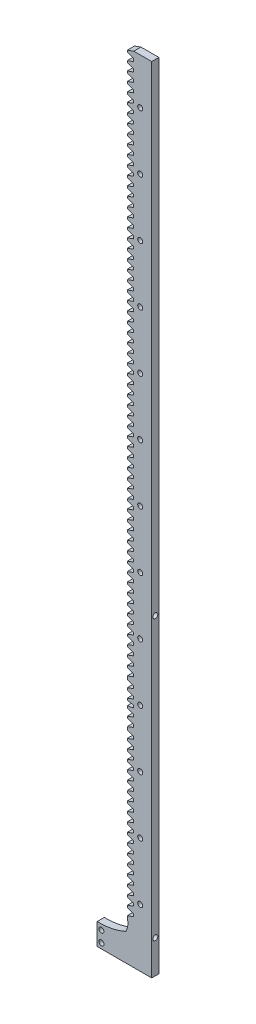
SolidWorks part; units mm, degrees
ref_plane "前视基准面" through (0, 0, 0) normal (0, 0, 1) x (1, 0, 0)
ref_plane "上视基准面" through (0, 0, 0) normal (0, 1, 0) x (1, 0, 0)
ref_plane "右视基准面" through (0, 0, 0) normal (1, 0, 0) x (0, 0, -1)
sketch "草图1" plane through (0, 0, 0) normal (0, 0, 1) x (1, 0, 0)
  line L0 (0, 0) -> (-38, 0)
  line L1 (-38, 0) -> (-38, 15)
  line L2 (-38, 15) -> (-10, 15) construction
  line L3 (-10, 95) -> (-10, 300) construction
  line L4 (-10, 300) -> (0, 300) construction
  line L5 (0, 300) -> (0, 0)
  line L6 (-12.5, 158.072) -> (-12.5, 156.352)
  line L7 (-12.5, 157.212) -> (-8.1615, 157.212) construction
  line L8 (-17, 143.0077) -> (-12.5, 144.6456)
  line L9 (-12.5, 139.2262) -> (-17, 140.864)
  line L10 (-12.5, 137.5024) -> (-12.5, 139.2262)
  line L11 (-17, 135.8646) -> (-12.5, 137.5024)
  line L12 (-17, 134.5808) -> (-17, 135.8646)
  line L13 (-12.5, 132.943) -> (-17, 134.5808)
  line L14 (-12.5, 131.2192) -> (-12.5, 132.943)
  line L15 (-17, 129.5814) -> (-12.5, 131.2192)
  line L16 (-17, 128.2977) -> (-17, 129.5814)
  line L17 (-12.5, 126.6598) -> (-17, 128.2977)
  line L18 (-12.5, 124.9361) -> (-12.5, 126.6598)
  line L19 (-17, 123.2982) -> (-12.5, 124.9361)
  line L20 (-17, 122.0145) -> (-17, 123.2982)
  line L21 (-12.5, 120.3766) -> (-17, 122.0145)
  line L22 (-12.5, 118.6529) -> (-12.5, 120.3766)
  line L23 (-17, 117.015) -> (-12.5, 118.6529)
  line L24 (-17, 115.7313) -> (-17, 117.015)
  line L25 (-12.5, 114.0934) -> (-17, 115.7313)
  line L26 (-12.5, 112.3697) -> (-12.5, 114.0934)
  line L27 (-17, 110.7318) -> (-12.5, 112.3697)
  line L28 (-17, 109.4481) -> (-17, 110.7318)
  line L29 (-12.5, 107.8102) -> (-17, 109.4481)
  line L30 (-12.5, 106.0865) -> (-12.5, 107.8102)
  line L31 (-17, 104.4486) -> (-12.5, 106.0865)
  line L32 (-17, 103.1649) -> (-17, 104.4486)
  line L33 (-12.5, 101.5271) -> (-17, 103.1649)
  line L34 (-12.5, 99.8033) -> (-12.5, 101.5271)
  line L35 (-17, 98.1654) -> (-12.5, 99.8033)
  line L36 (-17, 96.8817) -> (-17, 98.1654)
  line L37 (-12.5, 95.2439) -> (-17, 96.8817)
  line L38 (-12.5, 93.5201) -> (-12.5, 95.2439)
  line L39 (-17, 91.8823) -> (-12.5, 93.5201)
  line L40 (-17, 90.5985) -> (-17, 91.8823)
  line L41 (-12.5, 88.9607) -> (-17, 90.5985)
  line L42 (-12.5, 87.2369) -> (-12.5, 88.9607)
  line L43 (-17, 85.5991) -> (-12.5, 87.2369)
  line L44 (-17, 84.3154) -> (-17, 85.5991)
  line L45 (-12.5, 82.6775) -> (-17, 84.3154)
  line L46 (-12.5, 80.9538) -> (-12.5, 82.6775)
  line L47 (-17, 79.3159) -> (-12.5, 80.9538)
  line L48 (-17, 78.0322) -> (-17, 79.3159)
  line L49 (-12.5, 76.3943) -> (-17, 78.0322)
  line L50 (-12.5, 74.6706) -> (-12.5, 76.3943)
  line L51 (-17, 73.0327) -> (-12.5, 74.6706)
  line L52 (-17, 71.749) -> (-17, 73.0327)
  line L53 (-12.5, 70.1111) -> (-17, 71.749)
  line L54 (-12.5, 68.3874) -> (-12.5, 70.1111)
  line L55 (-17, 66.7495) -> (-12.5, 68.3874)
  line L56 (-17, 65.4658) -> (-17, 66.7495)
  line L57 (-12.5, 63.8279) -> (-17, 65.4658)
  line L58 (-12.5, 62.1042) -> (-12.5, 63.8279)
  line L59 (-17, 60.4663) -> (-12.5, 62.1042)
  line L60 (-17, 59.1826) -> (-17, 60.4663)
  line L61 (-12.5, 57.5448) -> (-17, 59.1826)
  line L62 (-12.5, 55.821) -> (-12.5, 57.5448)
  line L63 (-17, 54.1831) -> (-12.5, 55.821)
  line L64 (-17, 52.8994) -> (-17, 54.1831)
  line L65 (-12.5, 51.2616) -> (-17, 52.8994)
  line L66 (-12.5, 49.5378) -> (-12.5, 51.2616)
  line L67 (-17, 47.9) -> (-12.5, 49.5378)
  line L68 (-17, 46.6163) -> (-17, 47.9)
  line L69 (-12.5, 44.9784) -> (-17, 46.6163)
  line L70 (-12.5, 43.2546) -> (-12.5, 44.9784)
  line L71 (-17, 41.6168) -> (-12.5, 43.2546)
  line L72 (-17, 40.3331) -> (-17, 41.6168)
  line L73 (-12.5, 38.6952) -> (-17, 40.3331)
  line L74 (-12.5, 36.9715) -> (-12.5, 38.6952)
  line L75 (-17, 35.3336) -> (-12.5, 36.9715)
  line L76 (-17, 34.0499) -> (-17, 35.3336)
  line L77 (-12.5, 32.412) -> (-17, 34.0499)
  line L78 (-12.5, 30.6883) -> (-12.5, 32.412)
  line L79 (-17, 29.0504) -> (-12.5, 30.6883)
  line L80 (-17, 27.7667) -> (-17, 29.0504)
  line L81 (-12.5, 300.8615) -> (-12.5, 301.7215)
  line L82 (-12.5, 301.7215) -> (-10, 301.7215) construction
  line L83 (-12.5, 332.2737) -> (-12.5, 333.9937)
  line L84 (-17, 143.0077) -> (-17, 140.864)
  line L85 (-12.5, 300.8615) -> (-10, 300) construction
  line L86 (0, 332.2737) -> (0, 300)
  line L87 (-12.5, 333.1337) -> (-6.574, 333.1337) construction
  line L88 (-12.5, 338.5531) -> (-12.5, 340.2731)
  line L89 (-12.5, 339.4131) -> (-30.4802, 339.4131) construction
  line L90 (-12.5, 144.6456) -> (-12.5, 146.3694)
  line L91 (-12.5, 146.3694) -> (-17, 148.0072)
  line L92 (-17, 148.0072) -> (-17, 149.2909)
  line L93 (-17, 149.2909) -> (-12.5, 150.9288)
  line L94 (-12.5, 150.9288) -> (-12.5, 152.6525)
  line L95 (-12.5, 152.6525) -> (-17, 154.2904)
  line L96 (-17, 154.2904) -> (-17, 155.5741)
  line L97 (-17, 155.5741) -> (-12.5, 156.352)
  line L98 (-12.5, 338.5531) -> (-17, 336.9153)
  line L99 (-17, 336.9153) -> (-17, 335.6316)
  line L100 (-17, 335.6316) -> (-12.5, 333.9937)
  line L101 (-17, 406.0191) -> (-12.5, 407.6569)
  line L102 (-17, 404.7354) -> (-17, 406.0191)
  line L103 (0, 345.3332) -> (0, 332.2737)
  line L104 (-17, 330.6358) -> (-12.5, 332.2737)
  line L105 (-17, 329.3521) -> (-17, 330.6358)
  line L106 (-12.5, 327.7142) -> (-17, 329.3521)
  line L107 (-12.5, 325.9905) -> (-12.5, 327.7142)
  line L108 (-17, 324.3526) -> (-12.5, 325.9905)
  line L109 (-17, 323.0689) -> (-17, 324.3526)
  line L110 (-12.5, 321.4311) -> (-17, 323.0689)
  line L111 (-12.5, 319.7073) -> (-12.5, 321.4311)
  line L112 (-17, 318.0694) -> (-12.5, 319.7073)
  line L113 (-17, 316.7857) -> (-17, 318.0694)
  line L114 (-12.5, 315.1479) -> (-17, 316.7857)
  line L115 (-12.5, 313.4241) -> (-12.5, 315.1479)
  line L116 (-17, 311.7863) -> (-12.5, 313.4241)
  line L117 (-17, 310.5026) -> (-17, 311.7863)
  line L118 (-12.5, 308.8647) -> (-17, 310.5026)
  line L119 (-12.5, 307.1409) -> (-12.5, 308.8647)
  line L120 (-17, 305.5031) -> (-12.5, 307.1409)
  line L121 (-17, 304.2194) -> (-17, 305.5031)
  line L122 (-12.5, 302.5815) -> (-17, 304.2194)
  line L123 (-12.5, 302.5815) -> (-12.5, 301.7215)
  line L124 (-12.5, 403.0975) -> (-17, 404.7354)
  line L125 (-12.5, 401.3738) -> (-12.5, 403.0975)
  line L126 (-17, 399.7359) -> (-12.5, 401.3738)
  line L127 (-17, 398.4522) -> (-17, 399.7359)
  line L128 (-12.5, 396.8143) -> (-17, 398.4522)
  line L129 (-12.5, 395.0906) -> (-12.5, 396.8143)
  line L130 (-17, 393.4527) -> (-12.5, 395.0906)
  line L131 (-17, 392.169) -> (-17, 393.4527)
  line L132 (-12.5, 390.5311) -> (-17, 392.169)
  line L133 (-12.5, 388.8074) -> (-12.5, 390.5311)
  line L134 (-17, 387.1695) -> (-12.5, 388.8074)
  line L135 (-17, 385.8858) -> (-17, 387.1695)
  line L136 (-12.5, 384.2479) -> (-17, 385.8858)
  line L137 (-12.5, 382.5242) -> (-12.5, 384.2479)
  line L138 (-17, 380.8863) -> (-12.5, 382.5242)
  line L139 (-17, 379.6026) -> (-17, 380.8863)
  line L140 (-12.5, 377.9648) -> (-17, 379.6026)
  line L141 (-12.5, 376.2448) -> (-12.5, 377.1048)
  line L142 (-12.5, 376.2448) -> (-17, 374.6069)
  line L143 (-17, 374.6069) -> (-17, 373.3232)
  line L144 (-17, 373.3232) -> (-12.5, 371.6853)
  line L145 (-12.5, 371.6853) -> (-12.5, 369.9616)
  line L146 (-12.5, 369.9616) -> (-17, 368.3237)
  line L147 (-17, 368.3237) -> (-17, 367.04)
  line L148 (-17, 367.04) -> (-12.5, 365.4021)
  line L149 (-12.5, 365.4021) -> (-12.5, 363.6784)
  line L150 (-12.5, 363.6784) -> (-17, 362.0405)
  line L151 (-17, 362.0405) -> (-17, 360.7568)
  line L152 (-17, 360.7568) -> (-12.5, 359.1189)
  line L153 (-12.5, 359.1189) -> (-12.5, 357.3952)
  line L154 (-12.5, 357.3952) -> (-17, 355.7573)
  line L155 (-17, 355.7573) -> (-17, 354.4736)
  line L156 (-17, 354.4736) -> (-12.5, 352.8358)
  line L157 (-12.5, 352.8358) -> (-12.5, 351.112)
  line L158 (-12.5, 351.112) -> (-17, 349.4742)
  line L159 (-17, 349.4742) -> (-17, 348.1904)
  line L160 (-17, 348.1904) -> (-12.5, 346.5526)
  line L161 (-12.5, 346.5526) -> (-12.5, 344.8326)
  line L162 (-17, 343.1947) -> (-12.5, 344.8326)
  line L163 (-17, 341.911) -> (-17, 343.1947)
  line L164 (-12.5, 340.2731) -> (-17, 341.911)
  line L165 (-12.5, 407.6569) -> (-12.5, 409.3769)
  line L166 (-12.5, 408.5169) -> (-23.385, 408.5169) construction
  line L167 (-12.5, 377.9648) -> (-12.5, 377.1048)
  line L168 (-12.5, 439.0691) -> (-12.5, 439.9291)
  line L169 (-12.5, 452.4936) -> (-35.8093, 452.4936) construction
  line L170 (-12.5, 483.9058) -> (-28.5245, 483.9058) construction
  line L171 (-12.5, 451.6318) -> (-12.5, 453.3555)
  line L172 (-17, 449.9939) -> (-12.5, 451.6318)
  line L173 (-17, 448.7102) -> (-17, 449.9939)
  line L174 (-12.5, 447.0723) -> (-17, 448.7102)
  line L175 (-12.5, 445.3486) -> (-12.5, 447.0723)
  line L176 (-17, 443.7107) -> (-12.5, 445.3486)
  line L177 (-17, 442.427) -> (-17, 443.7107)
  line L178 (-12.5, 440.7891) -> (-17, 442.427)
  line L179 (-12.5, 440.7891) -> (-12.5, 439.9291)
  line L180 (-12.5, 439.0691) -> (-17, 437.4313)
  line L181 (-17, 437.4313) -> (-17, 436.1476)
  line L182 (-17, 436.1476) -> (-12.5, 434.5097)
  line L183 (-12.5, 434.5097) -> (-12.5, 432.7859)
  line L184 (-12.5, 432.7859) -> (-17, 431.1481)
  line L185 (-17, 431.1481) -> (-17, 429.8644)
  line L186 (-17, 429.8644) -> (-12.5, 428.2265)
  line L187 (-12.5, 428.2265) -> (-12.5, 426.5028)
  line L188 (-12.5, 426.5028) -> (-17, 424.8649)
  line L189 (-17, 424.8649) -> (-17, 423.5812)
  line L190 (-17, 423.5812) -> (-12.5, 421.9433)
  line L191 (-12.5, 421.9433) -> (-12.5, 420.2196)
  line L192 (-12.5, 420.2196) -> (-17, 418.5817)
  line L193 (-17, 418.5817) -> (-17, 417.298)
  line L194 (-17, 417.298) -> (-12.5, 415.6601)
  line L195 (-12.5, 415.6601) -> (-12.5, 413.9364)
  line L196 (-12.5, 413.9364) -> (-17, 412.2985)
  line L197 (-17, 412.2985) -> (-17, 411.0148)
  line L198 (-17, 411.0148) -> (-12.5, 409.3769)
  line L199 (-12.5, 515.318) -> (-35.8093, 515.318) construction
  line L200 (-12.5, 483.0439) -> (-12.5, 484.7677)
  line L201 (-17, 481.4061) -> (-12.5, 483.0439)
  line L202 (-17, 480.1224) -> (-17, 481.4061)
  line L203 (-12.5, 478.4845) -> (-17, 480.1224)
  line L204 (-12.5, 476.7608) -> (-12.5, 478.4845)
  line L205 (-17, 475.1229) -> (-12.5, 476.7608)
  line L206 (-17, 473.8392) -> (-17, 475.1229)
  line L207 (-12.5, 472.2013) -> (-17, 473.8392)
  line L208 (-12.5, 470.4776) -> (-12.5, 472.2013)
  line L209 (-17, 468.8397) -> (-12.5, 470.4776)
  line L210 (-17, 467.556) -> (-17, 468.8397)
  line L211 (-12.5, 465.9181) -> (-17, 467.556)
  line L212 (-12.5, 464.1981) -> (-12.5, 465.0581)
  line L213 (-12.5, 464.1981) -> (-17, 462.5603)
  line L214 (-17, 462.5603) -> (-17, 461.2766)
  line L215 (-17, 461.2766) -> (-12.5, 459.6387)
  line L216 (-12.5, 459.6387) -> (-12.5, 457.9149)
  line L217 (-12.5, 457.9149) -> (-17, 456.2771)
  line L218 (-17, 456.2771) -> (-17, 454.9934)
  line L219 (-17, 454.9934) -> (-12.5, 453.3555)
  line L220 (-12.5, 465.9181) -> (-12.5, 465.0581)
  line L221 (-12.5, 501.8935) -> (-12.5, 502.7535)
  line L222 (-17, 512.8183) -> (-12.5, 514.4561)
  line L223 (-17, 511.5346) -> (-17, 512.8183)
  line L224 (-12.5, 509.8967) -> (-17, 511.5346)
  line L225 (-12.5, 508.1729) -> (-12.5, 509.8967)
  line L226 (-17, 506.5351) -> (-12.5, 508.1729)
  line L227 (-17, 505.2514) -> (-17, 506.5351)
  line L228 (-12.5, 503.6135) -> (-17, 505.2514)
  line L229 (-12.5, 503.6135) -> (-12.5, 502.7535)
  line L230 (-12.5, 501.8935) -> (-17, 500.2556)
  line L231 (-17, 500.2556) -> (-17, 498.9719)
  line L232 (-17, 498.9719) -> (-12.5, 497.3341)
  line L233 (-12.5, 497.3341) -> (-12.5, 495.6103)
  line L234 (-12.5, 495.6103) -> (-17, 493.9724)
  line L235 (-17, 493.9724) -> (-17, 492.6887)
  line L236 (-17, 492.6887) -> (-12.5, 491.0509)
  line L237 (-12.5, 491.0509) -> (-12.5, 489.3271)
  line L238 (-12.5, 489.3271) -> (-17, 487.6893)
  line L239 (-17, 487.6893) -> (-17, 486.4056)
  line L240 (-17, 486.4056) -> (-12.5, 484.7677)
  line L241 (0, 345.3332) -> (0, 552.1515)
  line L242 (0, 552.1515) -> (-12.5, 552.1515)
  line L243 (-17, 550.5136) -> (-12.5, 552.1515)
  line L244 (-17, 549.2299) -> (-17, 550.5136)
  line L245 (-12.5, 547.5921) -> (-17, 549.2299)
  line L246 (-12.5, 545.8683) -> (-12.5, 547.5921)
  line L247 (-17, 544.2304) -> (-12.5, 545.8683)
  line L248 (-17, 542.9467) -> (-17, 544.2304)
  line L249 (-12.5, 541.3089) -> (-17, 542.9467)
  line L250 (-12.5, 539.5851) -> (-12.5, 541.3089)
  line L251 (-17, 537.9473) -> (-12.5, 539.5851)
  line L252 (-17, 536.6635) -> (-17, 537.9473)
  line L253 (-12.5, 535.0257) -> (-17, 536.6635)
  line L254 (-10.0528, 23.9832) -> (-10.0528, 22.8309) construction
  line L255 (-12.5, 533.3019) -> (-12.5, 535.0257)
  line L256 (-17, 531.6641) -> (-12.5, 533.3019)
  line L257 (-17, 530.3804) -> (-17, 531.6641)
  line L258 (-12.5, 528.7425) -> (-17, 530.3804)
  line L259 (-12.5, 527.0225) -> (-12.5, 527.8825)
  line L260 (-12.5, 527.0225) -> (-17, 525.3846)
  line L261 (-17, 525.3846) -> (-17, 524.1009)
  line L262 (-17, 524.1009) -> (-12.5, 522.4631)
  line L263 (-12.5, 522.4631) -> (-12.5, 520.7393)
  line L264 (-18.0028, 31.7521) -> (-18.0028, -9.9201) construction
  line L265 (-12.5, 520.7393) -> (-17, 519.1014)
  line L266 (-17, 519.1014) -> (-17, 517.8177)
  line L267 (-17, 517.8177) -> (-12.5, 516.1799)
  line L268 (-12.5, 516.1799) -> (-12.5, 514.4561)
  line L269 (-12.5, 528.7425) -> (-12.5, 527.8825)
  line L324 (-10, 15) -> (-10, 300) construction
  line L370 (-12.5, 300.8615) -> (-17, 299.2236)
  line L371 (-17, 299.2236) -> (-17, 297.9399)
  line L372 (-17, 297.9399) -> (-12.5, 296.3021)
  line L373 (-12.5, 296.3021) -> (-12.5, 294.5783)
  line L374 (-12.5, 294.5783) -> (-17, 292.9404)
  line L375 (-17, 292.9404) -> (-17, 291.6567)
  line L376 (-17, 291.6567) -> (-12.5, 290.0189)
  line L377 (-12.5, 290.0189) -> (-12.5, 288.2951)
  line L378 (-12.5, 288.2951) -> (-17, 286.6573)
  line L379 (-17, 286.6573) -> (-17, 285.3736)
  line L380 (-17, 285.3736) -> (-12.5, 283.7357)
  line L381 (-12.5, 283.7357) -> (-12.5, 282.0119)
  line L382 (-12.5, 282.0119) -> (-17, 280.3741)
  line L383 (-17, 280.3741) -> (-17, 279.0904)
  line L384 (-17, 279.0904) -> (-12.5, 277.4525)
  line L385 (-12.5, 277.4525) -> (-12.5, 275.7288)
  line L386 (-12.5, 275.7288) -> (-17, 274.0909)
  line L387 (-17, 274.0909) -> (-17, 272.8072)
  line L388 (-17, 272.8072) -> (-12.5, 271.1693)
  line L389 (-12.5, 271.1693) -> (-12.5, 269.4456)
  line L390 (-12.5, 269.4456) -> (-17, 267.8077)
  line L391 (-17, 267.8077) -> (-17, 266.524)
  line L392 (-17, 266.524) -> (-12.5, 264.8861)
  line L393 (-12.5, 264.8861) -> (-12.5, 263.1624)
  line L394 (-12.5, 263.1624) -> (-17, 261.5245)
  line L395 (-17, 261.5245) -> (-17, 260.2408)
  line L396 (-17, 260.2408) -> (-12.5, 258.6029)
  line L397 (-12.5, 258.6029) -> (-12.5, 256.8792)
  line L398 (-12.5, 256.8792) -> (-17, 255.2413)
  line L399 (-17, 255.2413) -> (-17, 253.9576)
  line L400 (-17, 253.9576) -> (-12.5, 252.3198)
  line L401 (-12.5, 252.3198) -> (-12.5, 250.596)
  line L402 (-12.5, 250.596) -> (-17, 248.9582)
  line L403 (-17, 248.9582) -> (-17, 247.6744)
  line L404 (-17, 247.6744) -> (-12.5, 246.0366)
  line L405 (-12.5, 246.0366) -> (-12.5, 244.3128)
  line L406 (-12.5, 244.3128) -> (-17, 242.675)
  line L407 (-17, 242.675) -> (-17, 241.3913)
  line L408 (-17, 241.3913) -> (-12.5, 239.7534)
  line L409 (-12.5, 239.7534) -> (-12.5, 238.0296)
  line L410 (-12.5, 238.0296) -> (-17, 236.3918)
  line L411 (-17, 236.3918) -> (-17, 235.1081)
  line L412 (-17, 235.1081) -> (-12.5, 233.4702)
  line L413 (-12.5, 233.4702) -> (-12.5, 231.7465)
  line L414 (-12.5, 231.7465) -> (-17, 230.1086)
  line L415 (-17, 230.1086) -> (-17, 228.8249)
  line L416 (-17, 228.8249) -> (-12.5, 227.187)
  line L417 (-12.5, 227.187) -> (-12.5, 225.4633)
  line L418 (-12.5, 225.4633) -> (-17, 223.8254)
  line L419 (-17, 223.8254) -> (-17, 222.5417)
  line L420 (-17, 222.5417) -> (-12.5, 220.9038)
  line L421 (-12.5, 220.9038) -> (-12.5, 219.1801)
  line L422 (-12.5, 219.1801) -> (-17, 217.5422)
  line L423 (-17, 217.5422) -> (-17, 216.2585)
  line L424 (-17, 216.2585) -> (-12.5, 214.6206)
  line L425 (-12.5, 214.6206) -> (-12.5, 212.8969)
  line L426 (-12.5, 212.8969) -> (-17, 211.259)
  line L427 (-17, 211.259) -> (-17, 209.9753)
  line L428 (-17, 209.9753) -> (-12.5, 208.3375)
  line L429 (-12.5, 208.3375) -> (-12.5, 206.6137)
  line L430 (-12.5, 206.6137) -> (-17, 204.9759)
  line L431 (-17, 204.9759) -> (-17, 203.6921)
  line L432 (-17, 203.6921) -> (-12.5, 202.0543)
  line L433 (-12.5, 202.0543) -> (-12.5, 200.3305)
  line L434 (-12.5, 200.3305) -> (-17, 198.6927)
  line L435 (-17, 198.6927) -> (-17, 197.409)
  line L436 (-17, 197.409) -> (-12.5, 195.7711)
  line L437 (-12.5, 195.7711) -> (-12.5, 194.0474)
  line L438 (-12.5, 194.0474) -> (-17, 192.4095)
  line L439 (-17, 192.4095) -> (-17, 191.1258)
  line L440 (-17, 191.1258) -> (-12.5, 189.4879)
  line L441 (-12.5, 189.4879) -> (-12.5, 187.7642)
  line L442 (-12.5, 187.7642) -> (-17, 186.1263)
  line L443 (-17, 186.1263) -> (-17, 184.8426)
  line L444 (-17, 184.8426) -> (-12.5, 183.2047)
  line L445 (-12.5, 183.2047) -> (-12.5, 181.481)
  line L446 (-12.5, 181.481) -> (-17, 179.8431)
  line L447 (-17, 179.8431) -> (-17, 178.5594)
  line L448 (-17, 178.5594) -> (-12.5, 176.9215)
  line L449 (-12.5, 176.9215) -> (-12.5, 175.1978)
  line L450 (-12.5, 175.1978) -> (-17, 173.5599)
  line L451 (-17, 173.5599) -> (-17, 171.4162)
  line L452 (-17, 171.4162) -> (-12.5, 169.7784)
  line L453 (-12.5, 169.7784) -> (-12.5, 168.0546)
  line L454 (-12.5, 168.0546) -> (-17, 166.4167)
  line L455 (-17, 166.4167) -> (-17, 165.133)
  line L456 (-17, 165.133) -> (-12.5, 163.4952)
  line L457 (-12.5, 163.4952) -> (-12.5, 161.7714)
  line L458 (-12.5, 161.7714) -> (-17, 160.1336)
  line L459 (-17, 160.1336) -> (-17, 158.8498)
  line L460 (-17, 158.8498) -> (-12.5, 158.072)
  line L463 (-10, 156.3501) -> (-10, 456.3501) construction
  arc A0 (-18.0028, 19.0416) -> (-38, 15) centre (-36.7849, 60.4805) cw
  arc A1 (-18.0028, 19.0416) -> (-17, 27.7667) centre (-28.5245, 24.671) ccw
  dimension "D1" = 7.95
  dimension "D8" = 0.86
  dimension "D2" = 15
  dimension "D3" = 10
  dimension "D4" = 300
  dimension "D5" = 1.7237
  dimension "D6" = 7
  dimension "D7" = 1.72
  dimension "D9" = 0.86
  dimension "D10" = 1.72
  dimension "D11" = 1.72
extrude "凸台-拉伸1" add sketch "草图1" along normal blind 5
sketch "草图2" plane through (0, 0, 5) normal (0, 0, 1) x (1, 0, 0)
  line L0 (-38, 7.5) -> (-22.7717, 7.5) construction
  line L1 (-38, 15) -> (-38, 0) construction
  circle A0 centre (-35, 11.3385) radius 1.75
  circle A1 centre (-35, 3.6615) radius 1.75
  circle A2 centre (15, 11) radius 1.75 construction
  circle A4 centre (15, 11) radius 1.75
  dimension "D1" = 3.5
  dimension "D2" = 3
extrude "切除-拉伸1" cut sketch "草图2" against normal blind 5
sketch "草图3" plane through (0, 0, 0) normal (1, 0, 0) x (0, 0, -1)
  circle A0 centre (-2.5, 213.6024) radius 1.75 construction
  circle A1 centre (-2.5, 23) radius 1.75 construction
  circle A2 centre (-2.5, 217) radius 1.75 construction
  circle A3 centre (-2.5, 23) radius 1.75
  circle A4 centre (-2.5, 217) radius 1.75
  dimension "D1" = 3.5
extrude "切除-拉伸2" cut sketch "草图3" against normal blind 10
sketch "草图4" plane through (0, 0, 5) normal (0, 0, 1) x (1, 0, 0)
  line L0 (0, 0) -> (0, 552.1515) construction
  circle A0 centre (-8, 320.3332) radius 1.75
  circle A1 centre (-8, 280.3332) radius 1.75
  circle A2 centre (-8, 240.3332) radius 1.75
  circle A3 centre (-8, 200.3332) radius 1.75
  circle A4 centre (-8, 160.3332) radius 1.75
  circle A5 centre (-8, 120.3332) radius 1.75
  circle A6 centre (-8, 80.3332) radius 1.75
  circle A7 centre (-8, 40.3332) radius 1.75
  circle A8 centre (-8, 360.3332) radius 1.75
  circle A9 centre (-8, 400.3332) radius 1.75
  circle A10 centre (-8, 440.3332) radius 1.75
  circle A11 centre (-8, 480.3332) radius 1.75
  circle A12 centre (-8, 520.3332) radius 1.75
  dimension "D1" = 3.5
  dimension "D2" = 8
  dimension "D3" = 6
  dimension "D4" = 8
extrude "切除-拉伸3" cut sketch "草图4" against normal blind 10
ref_plane "基准面1" through (0, 0, 2.5) normal (0, 0, 1) x (1, 0, 0)
